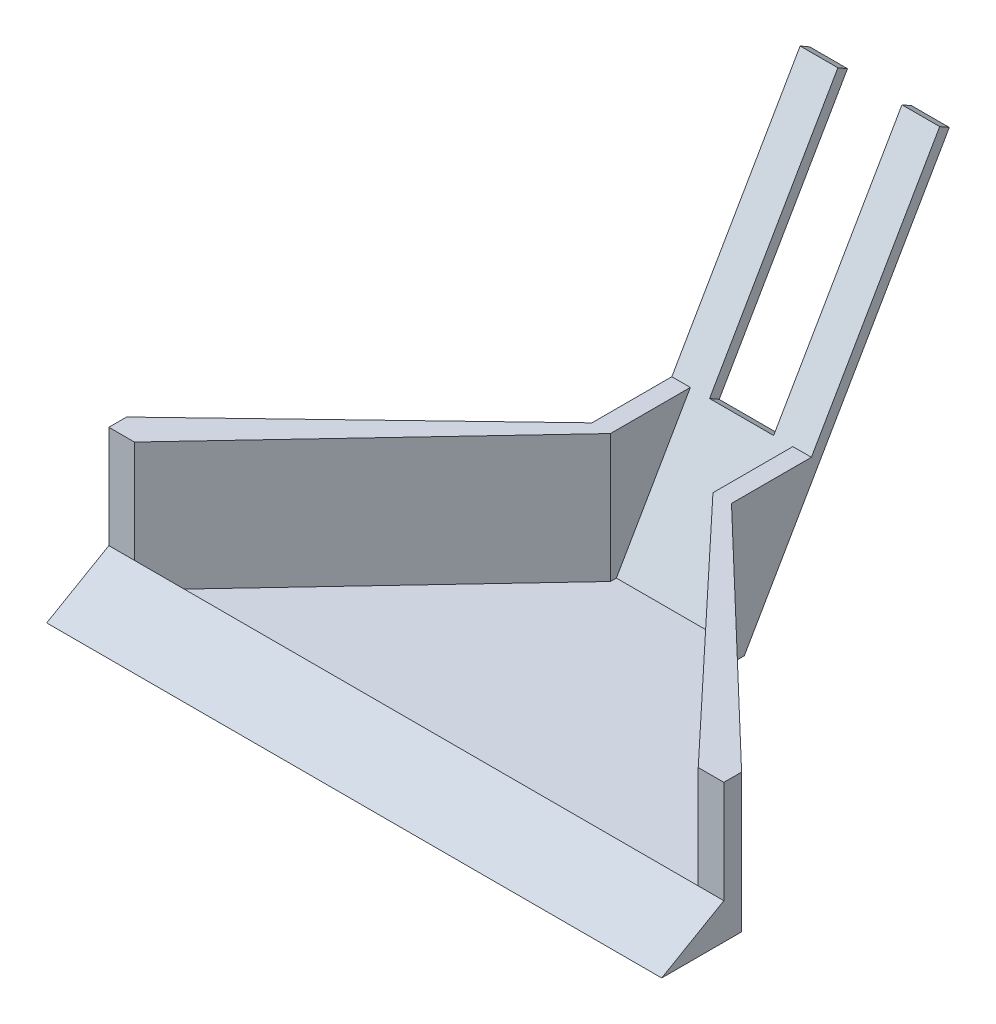
SolidWorks part; units mm, degrees
ref_plane "Front Plane" through (0, 0, 0) normal (0, 0, 1) x (1, 0, 0)
ref_plane "Top Plane" through (0, 0, 0) normal (0, 1, 0) x (1, 0, 0)
ref_plane "Right Plane" through (0, 0, 0) normal (1, 0, 0) x (0, 0, -1)
sketch "Sketch2" plane through (0, 0, 0) normal (0, 0, 1) x (1, 0, 0)
  line L1 (0, 0) -> (304.8, 0)
  line L2 (0, 0) -> (0, 17.78)
  line L3 (0, 17.78) -> (304.8, 17.78)
  line L4 (304.8, 0) -> (304.8, 17.78)
  line L5 (0, 0) -> (304.8, 17.78) construction
  line L6 (0, 17.78) -> (304.8, 0) construction
  point P4 (152.4, 8.89)
  dimension "D1" = 304.8
  dimension "D2" = 17.78
extrude "Boss-Extrude1" add sketch "Sketch2" along normal blind 152.4
sketch "Sketch3" plane through (304.8, 0, 0) normal (1, 0, 0) x (0, 0, -1)
  line L0 (-152.4, 0) -> (-121.6041, 17.78)
  line L1 (-152.4, 17.78) -> (0, 17.78) construction
  line L2 (-152.4, 0) -> (0, 0) construction
  line L3 (-152.4, 0) -> (-152.4, 17.78)
  line L4 (-152.4, 17.78) -> (-121.6041, 17.78)
  line L5 (-121.6041, 17.78) -> (-121.6041, 5.08)
  line L6 (-121.6041, 5.08) -> (0, 5.08)
  line L7 (0, 0) -> (0, 17.78) construction
  line L8 (0, 5.08) -> (0, 17.78)
  line L9 (0, 17.78) -> (-121.6041, 17.78)
  line M4 (0, 0) -> (0, 17.78)
  line M5 (0, 17.78) -> (-152.4, 17.78)
  line M6 (-152.4, 17.78) -> (-152.4, 0)
  dimension "D1" = 30
  dimension "D2" = 12.7
extrude "Cut-Extrude1" cut sketch "Sketch3" against normal through all contours L0 M6 M5 | L5 L6 M4 M5
sketch "Sketch4" plane through (0, 5.08, 0) normal (0, 1, 0) x (1, 0, 0)
  line L0 (0, -121.6041) -> (127, 0)
  line L1 (0, 0) -> (304.8, 0) construction
  line L2 (177.8, 0) -> (304.8, -121.6041)
  line L3 (0, 0) -> (127, 0)
  line L4 (177.8, 0) -> (304.8, 0)
  line L5 (0, -112.8126) -> (117.8183, 0)
  line L6 (0, -121.6041) -> (0, 0) construction
  line L7 (186.9817, 0) -> (304.8, -112.8126)
  line L8 (304.8, -121.6041) -> (304.8, 0) construction
  line L9 (0, -112.8126) -> (0, 0)
  line L10 (304.8, -112.8126) -> (304.8, 0)
  line M7 (304.8, -121.6041) -> (304.8, 0)
  line M8 (304.8, 0) -> (0, 0)
  line M9 (0, 0) -> (0, -121.6041)
  dimension "D1" = 50.8
  dimension "D2" = 6.35
  dimension "D3" = 6.35
extrude "Cut-Extrude2" cut sketch "Sketch4" against normal blind 203.2 contours L5 L3 M9 | L7 M8 M7
sketch "Sketch5" plane through (0, 5.08, 0) normal (0, 1, 0) x (1, 0, 0)
  line L1 (117.8183, 0) -> (186.9817, 0) construction
  line L9 (127, 0) -> (117.8183, 0)
  line L10 (117.8183, 0) -> (0, -112.8126)
  line L11 (0, -112.8126) -> (0, -121.6041)
  line L12 (177.8, 0) -> (186.9817, 0)
  line L13 (186.9817, 0) -> (304.8, -112.8126)
  line L14 (304.8, -112.8126) -> (304.8, -121.6041)
  line L18 (0, -121.6041) -> (304.8, -121.6041) construction
  line L19 (127, 0) -> (12.7, -121.6041)
  line L21 (177.8, 0) -> (292.1, -121.6041)
  line L22 (0, -121.6041) -> (12.7, -121.6041)
  line L23 (292.1, -121.6041) -> (304.8, -121.6041)
  dimension "D1" = 50.8
  dimension "D2" = 279.4
extrude "Boss-Extrude6" add sketch "Sketch5" along normal blind 63.5
sketch "Sketch8" plane through (0, 0, 0) normal (0, 0, -1) x (-1, 0, 0)
  line L0 (-186.9817, 68.58) -> (-186.9817, 0)
  line L1 (-186.9817, 0) -> (-117.8183, 0)
  line L2 (-117.8183, 0) -> (-117.8183, 68.58)
  line L3 (-117.8183, 68.58) -> (-127, 68.58)
  line L7 (-177.8, 68.58) -> (-186.9817, 68.58)
  line L9 (-177.8, 68.58) -> (-177.8, 5.08)
  line L10 (-177.8, 5.08) -> (-127, 5.08)
  line L11 (-127, 5.08) -> (-127, 68.58)
extrude "Boss-Extrude8" add sketch "Sketch8" along normal blind 76.2
sketch "Sketch10" plane through (186.9817, 0, 0) normal (1, 0, 0) x (0, 0, -1)
  line L4 (76.2, 0) -> (0, 0) construction
  line L5 (6.35, 0) -> (0, 0)
  line L7 (127, 219.9705) -> (133.35, 219.9705)
  line L9 (6.35, 0) -> (133.35, 219.9705)
  line L10 (0, 0) -> (127, 219.9705)
  dimension "D1" = 60
  dimension "D2" = 6.35
  dimension "D3" = 254
extrude "Boss-Extrude9" add sketch "Sketch10" against normal up to surface (69.1633 mm away) up to face at (117.8183, 34.29, -38.1)
sketch "Sketch12" plane through (0, 0, -76.2) normal (0, 0, -1) x (-1, 0, 0)
  line L0 (-186.9817, 0) -> (-186.9817, 68.58)
  line L1 (-186.9817, 68.58) -> (-177.8, 68.58)
  line L2 (-177.8, 68.58) -> (-177.8, 5.08)
  line L3 (-177.8, 5.08) -> (-127, 5.08)
  line L4 (-127, 5.08) -> (-127, 68.58)
  line L5 (-127, 68.58) -> (-117.8183, 68.58)
  line L6 (-117.8183, 68.58) -> (-117.8183, 0)
  line L7 (-117.8183, 0) -> (-186.9817, 0)
extrude "Cut-Extrude4" cut sketch "Sketch12" against normal up to surface (69.85 mm away)
sketch "Sketch13" plane through (0, -2.7496, -4.7625) normal (0, -0.5, -0.866) x (-1, 0, 0)
  line L0 (-186.9817, 130.175) -> (-117.8183, 130.175) construction
  line L1 (-186.9817, 3.175) -> (-186.9817, 257.175) construction
  line L2 (-117.8183, 257.175) -> (-117.8183, 3.175) construction
  line L3 (-117.8183, 257.175) -> (-186.9817, 257.175) construction
  dimension "D1" = 127
sketch "Sketch14" plane through (0, 0, 0) normal (0, 0.5, 0.866) x (1, 0, 0)
  line L2 (136.525, 79.1894) -> (168.275, 79.1894)
  line L3 (136.525, 79.1894) -> (136.525, 282.3894)
  line L4 (136.525, 282.3894) -> (168.275, 282.3894)
  line L5 (168.275, 79.1894) -> (168.275, 282.3894)
  line L6 (136.525, 79.1894) -> (168.275, 282.3894) construction
  line L7 (136.525, 282.3894) -> (168.275, 79.1894) construction
  line L8 (177.8, 79.1894) -> (168.275, 79.1894) construction
  line L9 (136.525, 79.1894) -> (127, 79.1894) construction
  point P8 (152.4, 180.7894)
  dimension "D1" = 31.75
  dimension "D2" = 203.2
extrude "Cut-Extrude5" cut sketch "Sketch14" against normal through all
sketch "Sketch15" plane through (0, 0, 0) normal (0, 0.5, 0.866) x (1, 0, 0)
  line L1 (117.8183, 206.375) -> (186.9817, 206.375)
  line L2 (117.8183, 206.375) -> (117.8183, 257.175)
  line L3 (117.8183, 257.175) -> (186.9817, 257.175)
  line L4 (186.9817, 206.375) -> (186.9817, 257.175)
  line L5 (117.8183, 206.375) -> (186.9817, 257.175) construction
  line L6 (117.8183, 257.175) -> (186.9817, 206.375) construction
  line L7 (186.9817, 254) -> (186.9817, 79.1894) construction
  line L8 (186.9817, 130.175) -> (117.8183, 130.175) construction
  line L9 (117.8183, 79.1894) -> (117.8183, 254) construction
  point P4 (152.4, 231.775)
  dimension "D1" = 76.2
  dimension "D2" = 50.8
extrude "Cut-Extrude6" cut sketch "Sketch15" against normal blind 12.7
